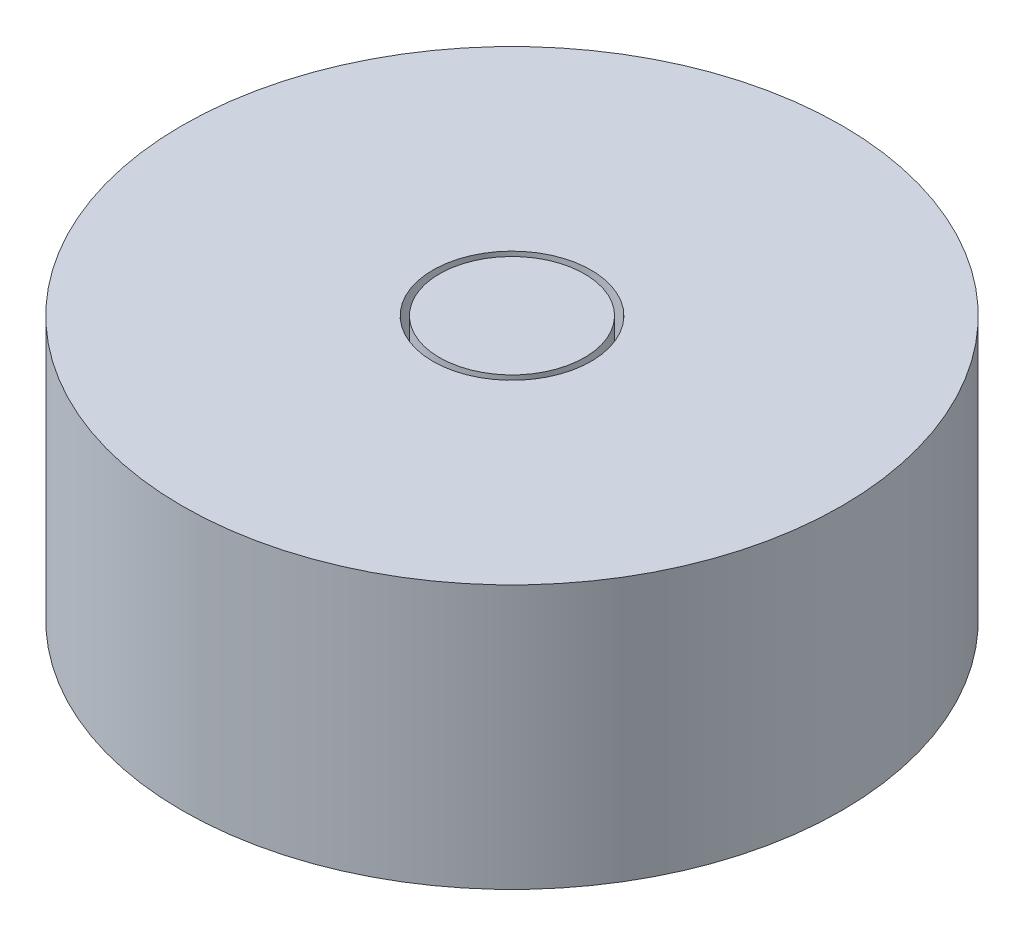
SolidWorks part; units mm, degrees
material "ABS"
ref_plane "Front Plane" through (0, 0, 0) normal (0, 0, 1) x (1, 0, 0)
ref_plane "Top Plane" through (0, 0, 0) normal (0, 1, 0) x (1, 0, 0)
ref_plane "Right Plane" through (0, 0, 0) normal (1, 0, 0) x (0, 0, -1)
sketch "Sketch1" plane through (0, 0, 0) normal (0, 1, 0) x (1, 0, 0)
  circle A0 centre (0, 0) radius 6.25
  dimension "D1" = 12.5
extrude "Extrude1" add sketch "Sketch1" along normal blind 5
sketch "Sketch2" plane through (0, 5, 0) normal (0, 1, 0) x (1, 0, 0)
  circle A0 centre (0, 0) radius 1.375
  circle A1 centre (0, 0) radius 1.5
  dimension "D1" = 3
  dimension "D2" = 2.75
extrude "Extrude2" cut sketch "Sketch2" against normal blind 1
